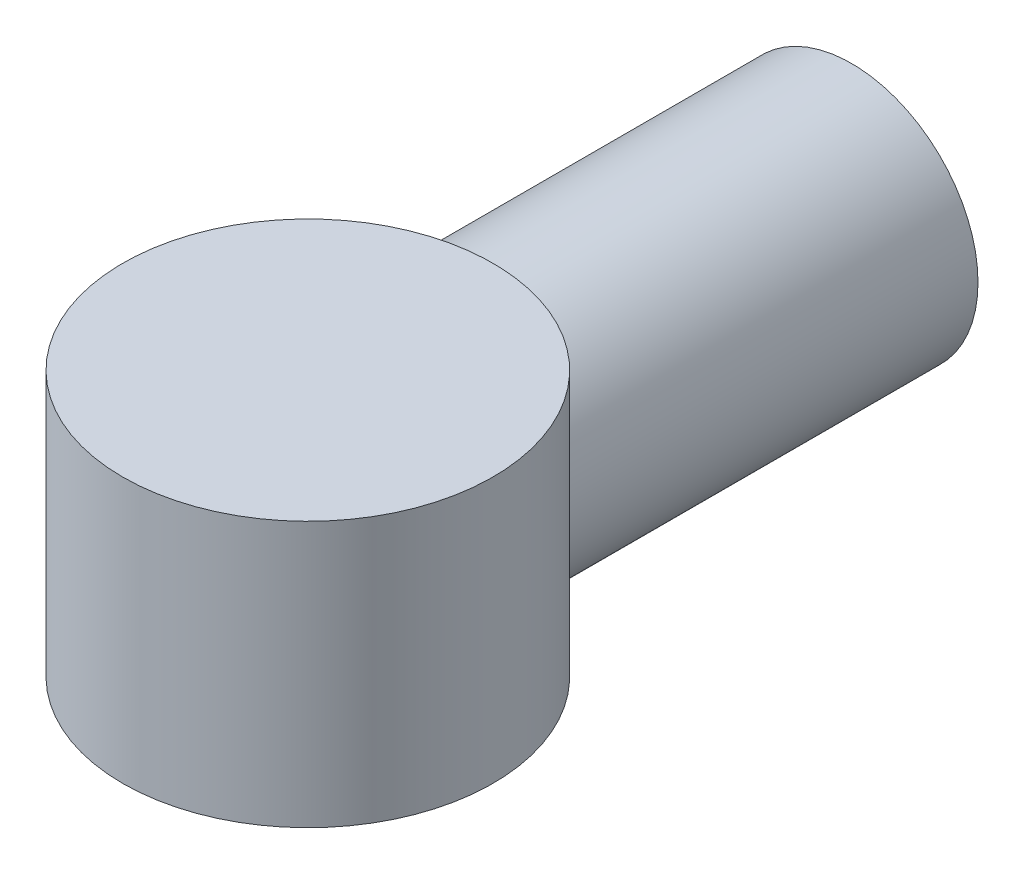
SolidWorks part; units mm, degrees
material "Ti-6Al-2Sn-2Zr-2Mo-2Cr-0.25Si (SS)"
ref_plane "Front Plane" through (0, 0, 0) normal (0, 0, 1) x (1, 0, 0)
ref_plane "Top Plane" through (0, 0, 0) normal (0, 1, 0) x (1, 0, 0)
ref_plane "Right Plane" through (0, 0, 0) normal (1, 0, 0) x (0, 0, -1)
sketch "Sketch1" plane through (0, 0, 0) normal (0, 0, 1) x (1, 0, 0)
  circle A0 centre (0, 0) radius 19
  circle A1 centre (0, 0) radius 23.8
  dimension "D1" = 47.6
  dimension "D2" = 38
extrude "Boss-Extrude1" add sketch "Sketch1" along normal blind 80
ref_plane "Plane1" through (0, 0, 80) normal (0, 0, 1) x (1, 0, 0)
sketch "Sketch3" plane through (0, 0, 80) normal (0, 0, 1) x (1, 0, 0)
  circle A1 centre (0, 0) radius 25
  dimension "D1" = 50
sketch "Sketch5" plane through (0, 0, 0) normal (0, 1, 0) x (1, 0, 0)
  circle A0 centre (0, -102.4735) radius 34.887
extrude "Boss-Extrude2" add sketch "Sketch5" along normal mid plane 50
